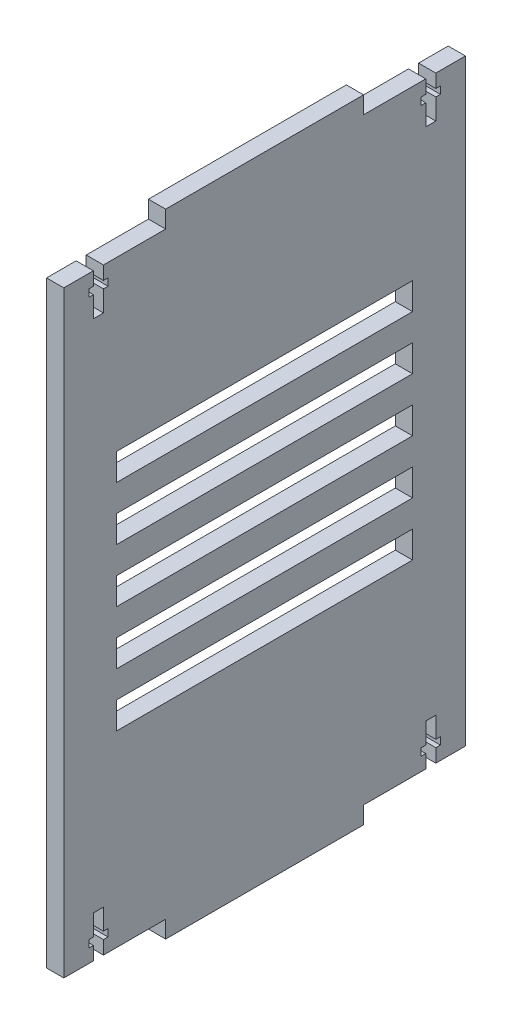
SolidWorks part; units mm, degrees
ref_plane "Front Plane" through (0, 0, 0) normal (0, 0, 1) x (1, 0, 0)
ref_plane "Top Plane" through (0, 0, 0) normal (0, 1, 0) x (1, 0, 0)
ref_plane "Right Plane" through (0, 0, 0) normal (1, 0, 0) x (0, 0, -1)
sketch "Sketch1" plane through (0, 0, 0) normal (1, 0, 0) x (0, 0, -1)
  line L1 (-35.6928, 37.9569) -> (83.7872, 37.9569)
  line L2 (-35.6928, 37.9569) -> (-35.6928, -139.8431)
  line L3 (-35.6928, -139.8431) -> (83.7872, -139.8431)
  line L4 (83.7872, 37.9569) -> (83.7872, -139.8431)
  dimension "D1" = 119.48
  dimension "D2" = 177.8
extrude "Boss-Extrude1" add sketch "Sketch1" along normal blind 5.13
sketch "Sketch2" plane through (5.13, 0, 0) normal (1, 0, 0) x (0, 0, -1)
  line L0 (-26.8928, 37.9569) -> (-23.8958, 37.9569)
  line L1 (83.7872, 37.9569) -> (-35.6928, 37.9569) construction
  line L2 (-23.8958, 37.9569) -> (-23.8958, 33.9619)
  line L3 (-23.8958, 33.9619) -> (-22.5368, 33.9619)
  line L4 (-22.5368, 33.9619) -> (-22.5368, 31.7949)
  line L5 (-22.5368, 31.7949) -> (-23.8958, 31.7949)
  line L6 (-23.8958, 31.7949) -> (-23.8958, 25.5879)
  line L7 (-23.8958, 25.5879) -> (-26.8928, 25.5879)
  line L8 (-26.8928, 25.5879) -> (-26.8928, 31.7949)
  line L9 (-26.8928, 31.7949) -> (-28.2518, 31.7949)
  line L10 (-28.2518, 31.7949) -> (-28.2518, 33.9619)
  line L11 (-28.2518, 33.9619) -> (-26.8928, 33.9619)
  line L12 (-26.8928, 33.9619) -> (-26.8928, 37.9569)
  line L13 (71.9872, 33.9619) -> (71.9872, 37.9569)
  line L14 (74.9842, 37.9569) -> (74.9842, 33.9619)
  line L15 (74.9842, 33.9619) -> (76.3432, 33.9619)
  line L16 (76.3432, 33.9619) -> (76.3432, 31.7949)
  line L17 (76.3432, 31.7949) -> (74.9842, 31.7949)
  line L18 (74.9842, 31.7949) -> (74.9842, 25.5879)
  line L19 (74.9842, 25.5879) -> (71.9872, 25.5879)
  line L20 (71.9872, 25.5879) -> (71.9872, 31.7949)
  line L21 (71.9872, 31.7949) -> (70.6282, 31.7949)
  line L22 (70.6282, 31.7949) -> (70.6282, 33.9619)
  line L23 (70.6282, 33.9619) -> (71.9872, 33.9619)
  line L24 (71.9872, 37.9569) -> (74.9842, 37.9569)
  line L25 (-35.6928, -50.9431) -> (83.7872, -50.9431) construction
  line L26 (-35.6928, 37.9569) -> (-35.6928, -139.8431) construction
  line L27 (83.7872, -139.8431) -> (83.7872, 37.9569) construction
  line L28 (76.3432, -133.6811) -> (74.9842, -133.6811)
  line L29 (76.3432, -135.8481) -> (76.3432, -133.6811)
  line L30 (74.9842, -135.8481) -> (76.3432, -135.8481)
  line L31 (74.9842, -139.8431) -> (74.9842, -135.8481)
  line L32 (71.9872, -139.8431) -> (74.9842, -139.8431)
  line L33 (71.9872, -135.8481) -> (71.9872, -139.8431)
  line L34 (70.6282, -135.8481) -> (71.9872, -135.8481)
  line L35 (70.6282, -133.6811) -> (70.6282, -135.8481)
  line L36 (71.9872, -133.6811) -> (70.6282, -133.6811)
  line L37 (71.9872, -127.4741) -> (71.9872, -133.6811)
  line L38 (74.9842, -127.4741) -> (71.9872, -127.4741)
  line L39 (74.9842, -133.6811) -> (74.9842, -127.4741)
  line L40 (-26.8928, -139.8431) -> (-23.8958, -139.8431)
  line L41 (-23.8958, -139.8431) -> (-23.8958, -135.8481)
  line L42 (-26.8928, -135.8481) -> (-26.8928, -139.8431)
  line L43 (-28.2518, -135.8481) -> (-26.8928, -135.8481)
  line L44 (-26.8928, -133.6811) -> (-28.2518, -133.6811)
  line L45 (-28.2518, -133.6811) -> (-28.2518, -135.8481)
  line L46 (-23.8958, -135.8481) -> (-22.5368, -135.8481)
  line L47 (-22.5368, -133.6811) -> (-23.8958, -133.6811)
  line L48 (-22.5368, -135.8481) -> (-22.5368, -133.6811)
  line L49 (-23.8958, -127.4741) -> (-26.8928, -127.4741)
  line L50 (-26.8928, -127.4741) -> (-26.8928, -133.6811)
  line L51 (-23.8958, -133.6811) -> (-23.8958, -127.4741)
  dimension "D1" = 2.167
  dimension "D2" = 2.997
  dimension "D3" = 2.997
  dimension "D4" = 3.995
  dimension "D5" = 3.995
  dimension "D6" = 1.359
  dimension "D7" = 1.359
  dimension "D8" = 6.207
  dimension "D9" = 6.207
  dimension "D10" = 1.359
  dimension "D12" = 8.8
  dimension "D11" = 2
extrude "Cut-Extrude1" cut sketch "Sketch2" against normal blind 5.13
sketch "Sketch3" plane through (0, 0, 0) normal (-1, 0, 0) x (0, 0, 1)
  line L0 (35.6928, 37.9569) -> (35.6928, -139.8431) construction
  line L1 (-68.0472, -12.0431) -> (19.9528, -12.0431)
  line L2 (-68.0472, -12.0431) -> (-68.0472, -20.0431)
  line L3 (-68.0472, -20.0431) -> (19.9528, -20.0431)
  line L4 (19.9528, -12.0431) -> (19.9528, -20.0431)
  line L5 (35.6928, 37.9569) -> (-83.7872, 37.9569) construction
  dimension "D1" = 8
  dimension "D2" = 88
  dimension "D3" = 15.74
  dimension "D4" = 50
extrude "Vents" cut sketch "Sketch3" against normal blind 5.13
pattern_linear "Vents pattern" count 5 spacing 16 along (0, -1, 0) of "Vents"
sketch "Sketch4" plane through (0, 37.9569, 0) normal (0, 1, 0) x (1, 0, 0)
  line L0 (5.13, 71.9872) -> (5.13, -23.8958) construction
  line L1 (0, 53.4872) -> (5.13, 53.4872)
  line L2 (0, 53.4872) -> (0, -5.3928)
  line L3 (0, -5.3928) -> (5.13, -5.3928)
  line L4 (5.13, 53.4872) -> (5.13, -5.3928)
  point P6 (0, 24.0472)
  dimension "D1" = 59.74
  dimension "D2" = 58.88
extrude "Boss-Extrude2" add sketch "Sketch4" along normal blind 5.13
sketch "Sketch5" plane through (0, -139.8431, 0) normal (0, -1, 0) x (1, 0, 0)
  line L0 (0, 23.8958) -> (0, -71.9872) construction
  line L1 (0, 5.3928) -> (5.13, 5.3928)
  line L2 (0, 5.3928) -> (0, -53.4872)
  line L3 (0, -53.4872) -> (5.13, -53.4872)
  line L4 (5.13, 5.3928) -> (5.13, -53.4872)
  line L5 (5.13, 23.8958) -> (5.13, -71.9872) construction
  point P8 (5.13, -24.0472)
  dimension "D1" = 59.74
  dimension "D2" = 58.88
extrude "Boss-Extrude3" add sketch "Sketch5" along normal blind 5.13
equation "\"D3@Sketch3\" = (\"D1@Sketch1\"-\"D2@Sketch3\")/2"
equation "\"D1@Sketch4\" = \"D1@Sketch1\"/2"
equation "\"D1@Sketch5\" = \"D1@Sketch1\"/2"
